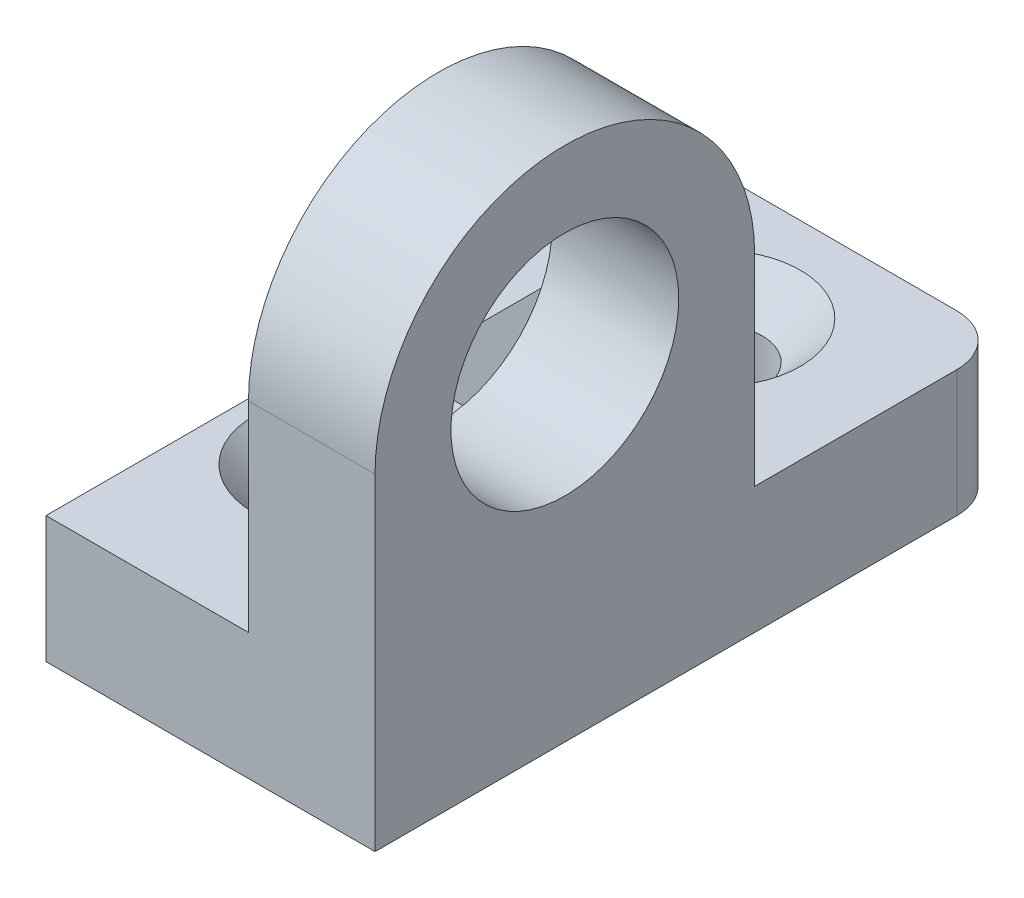
SolidWorks part; units mm, degrees
ref_plane "前视基准面" through (0, 0, 0) normal (0, 0, 1) x (1, 0, 0)
ref_plane "上视基准面" through (0, 0, 0) normal (0, 1, 0) x (1, 0, 0)
ref_plane "右视基准面" through (0, 0, 0) normal (1, 0, 0) x (0, 0, -1)
sketch "草图1" plane through (0, 0, 0) normal (1, 0, 0) x (0, 0, -1)
  line L2 (7.5, 0) -> (7.5, -12.92)
  line L3 (7.5, -12.92) -> (-7.5, -12.92)
  line L4 (-7.5, 0) -> (-7.5, -12.92)
  circle A0 centre (0, 0) radius 4.5
  arc A1 (7.5, 0) -> (-7.5, 0) centre (0, 0) ccw
  dimension "D1" = 9
  dimension "D2" = 7.5
  dimension "D3" = 12.92
extrude "凸台-拉伸1" add sketch "草图1" along normal blind 5
sketch "草图2" plane through (0, -12.92, 0) normal (0, -1, 0) x (1, 0, 0)
  line L0 (5, -7.5) -> (5, 7.5) construction
  line L1 (5, 7.5) -> (-8, 7.5)
  line L2 (5, 7.5) -> (5, -17.5)
  line L3 (5, -17.5) -> (-8, -17.5)
  line L4 (-8, 7.5) -> (-8, -17.5)
  line L5 (5, -7.5) -> (0, -7.5) construction
  line L6 (5, 7.5) -> (0, 7.5) construction
  dimension "D1" = 13
  dimension "D2" = 10
extrude "凸台-拉伸2" add sketch "草图2" against normal blind 5
sketch "草图3" plane through (0, 0, -7.5) normal (0, 0, -1) x (-1, 0, 0)
  line L0 (0, -1.92) -> (6, -7.92)
  line L1 (0, -7.92) -> (0, 0) construction
  line L2 (8, -7.92) -> (-5, -7.92) construction
  dimension "D1" = 6
  dimension "D2" = 6
rib "筋1" sketch "草图3" sketch "草图3" thickness 3 extrusion direction parallel to sketch draft on no parameters "D1"=3
hole_wizard "打孔尺寸(%根据十字)槽半沉头木螺钉的类型1" positions "草图6" profile "草图7" countersink size "M3" standard "GB" end condition through all
sketch "草图6" plane through (0, -7.92, 0) normal (0, 1, 0) x (1, 0, 0)
  line L1 (0, 7.5) -> (-6, 7.5) construction
  line L2 (5, 17.5) -> (5, 7.5) construction
  point P0 (-1.5, 12.5)
  point P2 (-4, 0)
  dimension "D1" = 4
  dimension "D2" = 5
  dimension "D3" = 6.5
sketch "草图7" plane through (-1.5, -7.92, -12.5) normal (1, 0, 0) x (0, 0, 1)
  line L0 (0, 0) -> (0, 5)
  line L1 (0, 5) -> (1.8, 5)
  line L2 (1.8, 5) -> (1.8, 1.5)
  line L3 (1.8, 1.5) -> (3.3, 0)
  line L5 (3.3, 0) -> (0, 0)
  line L6 (-1.8, 1.5) -> (-3.3, 0) construction
  line L11 (0, -6.35) -> (0, 107.95) construction
  dimension "通孔孔直径" = 3.6
  dimension "通孔孔深度" = 5
  dimension "近端锥形沉头孔直径" = 6.6
  dimension "近端锥形沉头孔角度" = 90
fillet "圆角1" radius 2 1 edges at (5, -10.42, -17.5)
